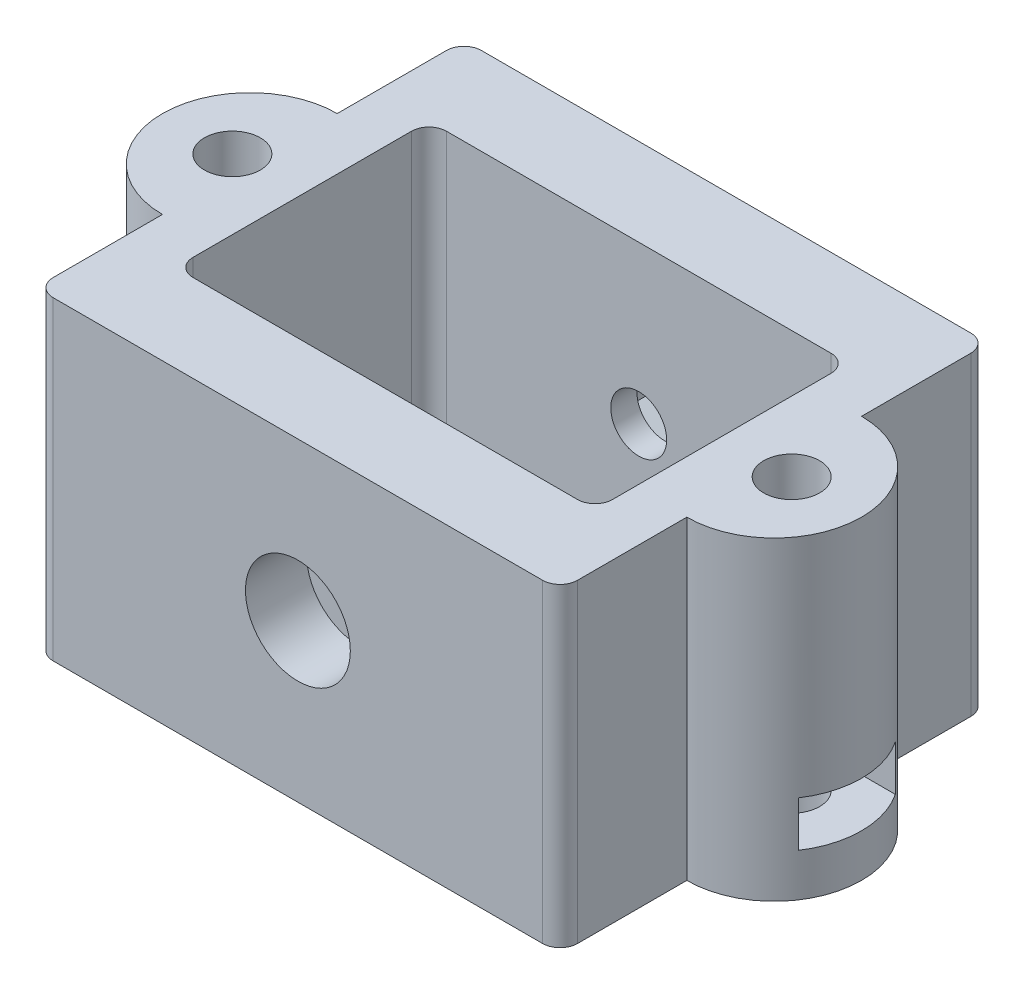
SolidWorks part; units mm, degrees
ref_plane "Front Plane" through (0, 0, 0) normal (0, 0, 1) x (1, 0, 0)
ref_plane "Top Plane" through (0, 0, 0) normal (0, 1, 0) x (1, 0, 0)
ref_plane "Right Plane" through (0, 0, 0) normal (1, 0, 0) x (0, 0, -1)
sketch "Sketch1" plane through (0, 0, 0) normal (0, 1, 0) x (1, 0, 0)
  line L0 (15, 24.5) -> (15, 0) construction
  line L1 (0, 0) -> (30, 0)
  line L2 (0, 0) -> (0, 7.25)
  line L3 (0, 24.5) -> (30, 24.5)
  line L4 (30, 0) -> (30, 7.25)
  line L5 (30, 17.25) -> (30, 24.5)
  line L6 (3, 19.5) -> (27, 19.5)
  line L7 (3, 19.5) -> (3, 5)
  line L8 (3, 5) -> (27, 5)
  line L9 (27, 19.5) -> (27, 5)
  line L10 (3, 19.5) -> (27, 5) construction
  line L11 (3, 5) -> (27, 19.5) construction
  line L12 (30, 12.25) -> (15, 12.25) construction
  line L13 (30, 17.25) -> (30, 12.25) construction
  line L14 (0, 17.25) -> (0, 24.5)
  line L15 (0, 12.25) -> (15, 12.25) construction
  line L16 (0, 17.25) -> (0, 12.25) construction
  arc A0 (30, 17.25) -> (30, 7.25) centre (30, 12.25) cw
  arc A1 (0, 17.25) -> (0, 7.25) centre (0, 12.25) ccw
  point P7 (15, 12.25)
  point P9 (15, 12.25)
  dimension "D1" = 30
  dimension "D2" = 24.5
  dimension "D3" = 5
  dimension "D4" = 3
  dimension "D5" = 10
extrude "Boss-Extrude1" add sketch "Sketch1" along normal blind 18
sketch "Sketch2" plane through (0, 0, 0) normal (0, -1, 0) x (1, 0, 0)
  line L0 (15, -19.5) -> (15, -5) construction
  line L2 (27, -19.5) -> (3, -19.5) construction
  line L3 (3, -5) -> (27, -5) construction
  line L4 (31, -12.25) -> (15, -12.25) construction
  circle A2 centre (31, -12.25) radius 1.6
  circle A4 centre (-1, -12.25) radius 1.6
  dimension "D1" = 3.2
  dimension "D2" = 32
extrude "Cut-Extrude1" cut sketch "Sketch2" against normal through all
sketch "Sketch3" plane through (0, 0, -24.5) normal (0, 0, -1) x (-1, 0, 0)
  line L0 (-15, 18) -> (-15, 0) construction
  line L1 (-30, 18) -> (0, 18) construction
  line L2 (-30, 0) -> (0, 0) construction
  circle A0 centre (-15, 9) radius 1.6
  dimension "D1" = 3.2
extrude "Cut-Extrude2" cut sketch "Sketch3" against normal through all
sketch "Sketch4" plane through (0, 0, 0) normal (0, 0, 1) x (1, 0, 0)
  circle A0 centre (15, 9) radius 3
  dimension "D1" = 6
extrude "Cut-Extrude3" cut sketch "Sketch4" against normal blind 3.5
sketch "Sketch5" plane through (0, 0, -24.5) normal (0, 0, -1) x (-1, 0, 0)
  line L1 (-12.2287, 7.4) -> (-12.2287, 10.6)
  line L2 (-12.2287, 10.6) -> (-15, 12.2)
  line L3 (-15, 12.2) -> (-17.7713, 10.6)
  line L4 (-17.7713, 10.6) -> (-17.7713, 7.4)
  line L5 (-17.7713, 7.4) -> (-15, 5.8)
  line L6 (-15, 5.8) -> (-12.2287, 7.4)
  line L8 (-30, 18) -> (-30, 0) construction
  circle A0 centre (-15, 9) radius 2.7713 construction
  dimension "D1" = 6.4
extrude "Cut-Extrude4" cut sketch "Sketch5" against normal blind 3.5
fillet "Fillet1" radius 1 8 edges at (30, 9, -24.5) (30, 9, 0) (0, 9, 0) (0, 9, -24.5) (27, 9, -5) (3, 9, -5) (3, 9, -19.5) (27, 9, -19.5)
ref_plane "Plane1" through (0, 2.46, 0) normal (0, -1, 0) x (-1, 0, 0)
sketch "Sketch6" plane through (0, 2.46, 0) normal (0, -1, 0) x (-1, 0, 0)
  line L0 (-32.6, 15.0213) -> (-42.6, 15.0213)
  line L10 (-29, 24.5) -> (-1, 24.5) construction
  line L11 (-29.4, 9.4787) -> (-27.8, 12.25)
  line L12 (-27.8, 12.25) -> (-29.4, 15.0213)
  line L13 (-29.4, 15.0213) -> (-32.6, 15.0213)
  line L16 (-32.6, 9.4787) -> (-29.4, 9.4787)
  line L17 (-32.6, 15.0213) -> (-32.6, 9.4787) construction
  line L18 (-42.6, 15.0213) -> (-42.6, 9.4787)
  line L19 (-33.15, 14.0687) -> (-33.95, 12.683) [skipped]
  line L20 (-33.15, 10.4313) -> (-32.35, 9.0457) [skipped]
  line L21 (-42.6, 9.4787) -> (-32.6, 9.4787)
  line L22 (-0.6, 15.0213) -> (2.6, 15.0213)
  line L23 (-15, 19.5) -> (-15, 5) construction
  line L24 (-26, 19.5) -> (-4, 19.5) construction
  line L25 (-4, 5) -> (-26, 5) construction
  line L26 (-2.2, 12.25) -> (-0.6, 15.0213)
  line L27 (-0.6, 9.4787) -> (-2.2, 12.25)
  line L28 (2.6, 9.4787) -> (-0.6, 9.4787)
  line L29 (12.6, 9.4787) -> (2.6, 9.4787)
  line L30 (12.6, 15.0213) -> (12.6, 9.4787)
  line L31 (2.6, 15.0213) -> (12.6, 15.0213)
  arc A0 (-32.6, 9.9873) -> (-32.6, 14.5127) centre (-31, 12.25) ccw construction
  point P8 (0, 0)
  point P17 (0, 0)
  dimension "D1" = 6.4
  dimension "D2" = 10
extrude "Cut-Extrude5" cut sketch "Sketch6" against normal blind 2.6
